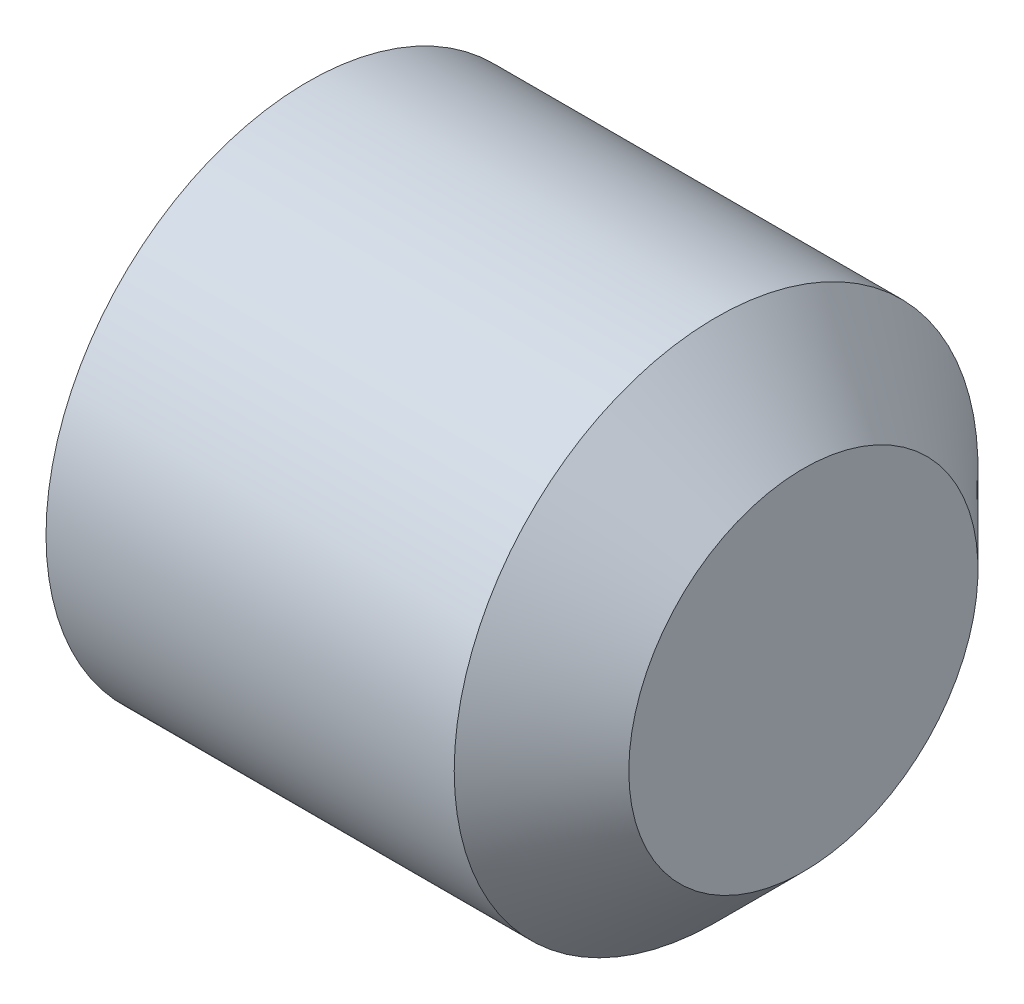
SolidWorks part; units mm, degrees
revolve "BaseBody" add sketch "BodySke" angle 360 about L5
sketch "BodySke" plane through (0, 0, 0) normal (0, 0, 1) x (1, 0, 0)
  line L0 (0, 0) -> (0, 1.2195)
  line L1 (0, 1.2195) -> (0.1619, 1.5)
  line L2 (0.1619, 1.5) -> (2.5, 1.5)
  line L3 (2.5, 1.5) -> (3, 1)
  line L4 (3, 0) -> (0, 0)
  line L5 (-12.7, 0) -> (88.9, 0) construction
  line L6 (3, 1) -> (3, 0)
  line L7 (3, 1) -> (3, 10.525) construction
  line L8 (0, -1.2195) -> (0.1619, -1.5) construction
  line L9 (0.5, 15.875) -> (0.5, -3.175) construction
  line L10 (2.5, -1.5) -> (3, -1) construction
  dimension "Diameter" = 3
  dimension "Drive_ch_ang" = 60
  dimension "Minor_dia" = 2.439
  dimension "Cup_nose_ang" = 45
  dimension "Cup_dia" = 2
  dimension "Length" = 3
  dimension "Advance" = 0.5
cosmetic thread "ThreadCosmetic" [suppressed] parameters "Thread_minor"=2.439
ref_plane "Plane1" through (0, 0, 0) normal (0, 0, 1) x (1, 0, 0)
ref_plane "Plane2" through (0, 0, 0) normal (0, 1, 0) x (1, 0, 0)
ref_plane "Plane3" through (0, 0, 0) normal (1, 0, 0) x (0, 0, -1)
sketch "Sketch2" plane through (0, 0, 0) normal (-1, 0, 0) x (0, 0, 1)
  line L0 (0.433, 0.75) -> (-0.433, 0.75)
  line L1 (-0.433, 0.75) -> (-0.866, 0)
  line L2 (0.433, 0.75) -> (0.866, 0)
  line L3 (0.433, -0.75) -> (0.866, 0)
  line L4 (0.433, -0.75) -> (-0.433, -0.75)
  line L5 (-0.433, -0.75) -> (-0.866, 0)
  dimension "Hex_size" = 1.5
  dimension "D2" = 0.75
  dimension "D3" = 0.75
extrude "Hex" cut sketch "Sketch2" against normal blind 1.2
sketch "ThdSchSke" plane through (0, 0, 0) normal (0, 0, 1) x (1, 0, 0)
  line L0 (0.1619, -1.2195) -> (-0.0345, -1.5)
  line L1 (0.1619, -1.2195) -> (0.3584, -1.5)
  line L2 (0.3584, -1.5) -> (0.3584, -1.875)
  line L3 (-3.175, 0) -> (5.1513, 0) construction
  line L5 (0.3584, -1.875) -> (-0.0345, -1.875)
  line L6 (-0.0345, -1.875) -> (-0.0345, -1.5)
  line L8 (0.1619, 1.5) -> (0.1619, -1.5) construction
  dimension "Thread_minor" = 2.439
  dimension "Diameter" = 3
revolve "ThreadSchematic" [suppressed] cut sketch "ThdSchSke" angle 360 about L3
pattern_linear "ThdSchPat" [suppressed]
equation "\"D2@Sketch2\" = \"Hex_size@Sketch2\" / 2"
equation "\"D3@Sketch2\" = \"Hex_size@Sketch2\" / 2"
equation "\"Thread_minor@ThreadCosmetic\" = \"Minor_dia@BodySke\""
equation "\"Thread_minor@ThdSchSke\" = \"Thread_minor@ThreadCosmetic\""
equation "\"Diameter@ThdSchSke\" = \"Diameter@BodySke\""
equation "\"Overcut@ThdSchSke\" = \"Diameter@BodySke\" * 1.25"
equation "\"Num_threads@ThdSchPat\" = int( (\"Length@BodySke\" - ( ( ( \"Diameter@BodySke\" - \"Minor_dia@BodySke\" ) * 0.5 ) / tan( \"Drive_ch_ang@BodySke\" * 0.017453292 ) ) - ( ( ( \"Diameter@BodySke\" - \"Cup_dia@BodySke\" ) * 0.5 ) * tan( \"Cup_nose_ang@BodySke\" * 0.017453292 ) ) ) / \"Advance@BodySke\" + 0.999 )  + 1"
equation "\"Advance@ThdSchPat\" = (\"Length@BodySke\" - ( ( ( \"Diameter@BodySke\" - \"Minor_dia@BodySke\" ) * 0.5 ) / tan( \"Drive_ch_ang@BodySke\" * 0.017453292 ) ) - ( ( ( \"Diameter@BodySke\" - \"Cup_dia@BodySke\" ) * 0.5 ) * tan( \"Cup_nose_ang@BodySke\" * 0.017453292 ) ) ) /  (\"Num_threads@ThdSchPat\" - 1) 'relax it"
equation "' \"Num_threads@ThdSchPat\" = \"Num_threads@ThdSchPat\" - sgn( \"Num_threads@ThdSchPat\" - 1) '---chamfered tips only---"
